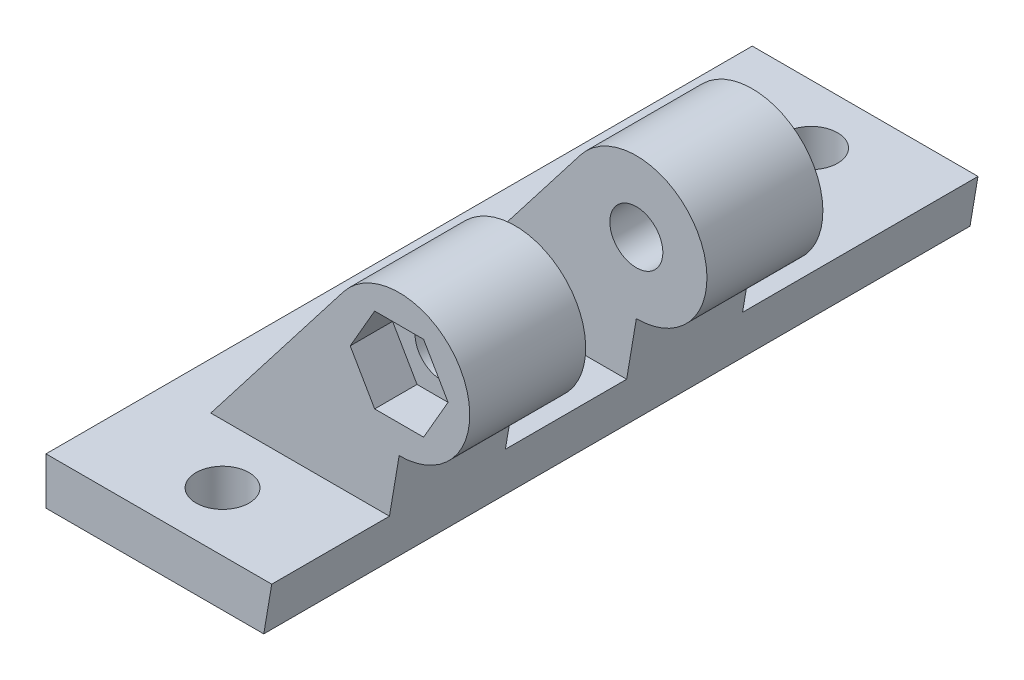
SolidWorks part; units mm, degrees
ref_plane "Front Plane" through (0, 0, 0) normal (0, 0, 1) x (1, 0, 0)
ref_plane "Top Plane" through (0, 0, 0) normal (0, 1, 0) x (1, 0, 0)
ref_plane "Right Plane" through (0, 0, 0) normal (1, 0, 0) x (0, 0, -1)
sketch "Sketch1" plane through (0, 0, 0) normal (0, 1, 0) x (1, 0, 0)
  line L0 (0, 30) -> (0, -30) construction
  line L1 (-10, -30) -> (10, -30)
  line L2 (-10, -30) -> (-10, 30)
  line L3 (-10, 30) -> (10, 30)
  line L4 (10, -30) -> (10, 30)
  line L5 (-10, -30) -> (10, 30) construction
  line L6 (-10, 30) -> (10, -30) construction
  circle A0 centre (0, 25) radius 2.25
  circle A1 centre (0, -25) radius 2.25
  point P0 (0, 0)
  dimension "D3" = 5
  dimension "D4" = 4.5
  dimension "D5" = 5
  dimension "D6" = 4.5
  dimension "D1" = 20
  dimension "D2" = 60
extrude "Boss-Extrude1" add sketch "Sketch1" along normal blind 5
ref_plane "Plane1" through (0, 0, 20) normal (0, 0, 1) x (1, 0, 0)
ref_plane "Plane2" through (0, 0, -10) normal (0, 0, -1) x (-1, 0, 0)
sketch "Sketch2" plane through (0, 0, 20) normal (0, 0, 1) x (1, 0, 0)
  line L0 (10, 5) -> (10, 0) construction
  line L1 (10, 9.8653) -> (10, 5)
  line L2 (10, 5) -> (-6, 5)
  line L3 (-10, 5) -> (10, 5) construction
  line L4 (-6, 5) -> (5.2557, 19.5384)
  circle A0 centre (10, 15.8653) radius 2.25
  arc A1 (10, 9.8653) -> (5.2557, 19.5384) centre (10, 15.8653) ccw
  dimension "D1" = 4.5
  dimension "D2" = 12
  dimension "D3" = 0
  dimension "D4" = 16
extrude "Boss-Extrude2" add sketch "Sketch2" against normal blind 9.85
sketch "Sketch3" plane through (0, 0, -10) normal (0, 0, -1) x (-1, 0, 0)
  line L0 (-10, 9.8653) -> (-10, 5)
  line L1 (-10, 5) -> (6, 5)
  line L2 (6, 5) -> (-5.2934, 19.5866)
  circle A0 centre (-10, 15.8653) radius 2.25
  arc A2 (-5.2934, 19.5866) -> (-10, 9.8653) centre (-10, 15.8653) ccw
  dimension "D1" = 4.5
extrude "Boss-Extrude3" add sketch "Sketch3" against normal blind 9.85
sketch "Sketch4" plane through (0, 0, 0) normal (0, -1, 0) x (1, 0, 0)
  line L1 (-15.4249, 34.5056) -> (18.4021, 34.5056)
  line L2 (-15.4249, 34.5056) -> (-15.4249, -38.0625)
  line L3 (-15.4249, -38.0625) -> (18.4021, -38.0625)
  line L4 (18.4021, 34.5056) -> (18.4021, -38.0625)
extrude "Cut-Extrude1" cut sketch "Sketch4" against normal blind 1
sketch "Sketch5" plane through (0, 0, -30) normal (0, 0, -1) x (-1, 0, 0)
  line L0 (-10, 9.8653) -> (-10, 1)
  line L1 (-10, 1) -> (-8.5, 1)
  line L2 (10, 1) -> (-10, 1) construction
  line L3 (-8.5, 1) -> (-10, 9.8653)
  dimension "D1" = 1.5
extrude "Cut-Extrude2" cut sketch "Sketch5" against normal through all
sketch "Sketch6" plane through (0, 0, 20) normal (0, 0, 1) x (1, 0, 0)
  line L0 (8.5, 1) -> (-10, 1) construction
  line L1 (12.0785, 12.2653) -> (14.1569, 15.8653)
  line L2 (14.1569, 15.8653) -> (12.0785, 19.4653)
  line L3 (12.0785, 19.4653) -> (7.9215, 19.4653)
  line L4 (7.9215, 19.4653) -> (5.8431, 15.8653)
  line L5 (5.8431, 15.8653) -> (7.9215, 12.2653)
  line L6 (7.9215, 12.2653) -> (12.0785, 12.2653)
  circle A0 centre (10, 15.8653) radius 3.6 construction
  dimension "D1" = 7.2
extrude "Cut-Extrude3" cut sketch "Sketch6" against normal blind 3.6
